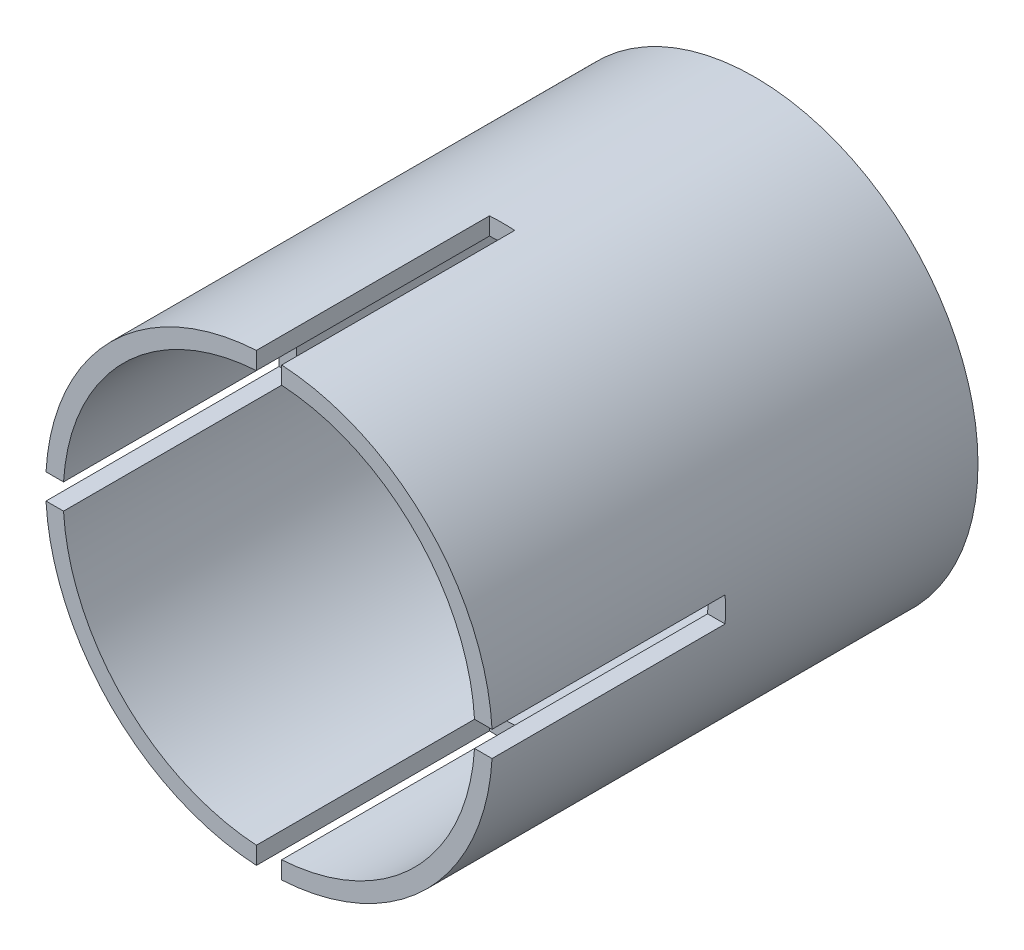
SolidWorks part; units mm, degrees
ref_plane "正面" through (0, 0, 0) normal (0, 0, 1) x (1, 0, 0)
ref_plane "平面" through (0, 0, 0) normal (0, 1, 0) x (1, 0, 0)
ref_plane "右側面" through (0, 0, 0) normal (1, 0, 0) x (0, 0, -1)
sketch "ｽｹｯﾁ1" plane through (0, 0, 0) normal (0, 0, 1) x (1, 0, 0)
  circle A0 centre (0, 0) radius 10.6
  circle A1 centre (0, 0) radius 11.5
  dimension "D1" = 21.2
  dimension "D2" = 23
extrude "ﾎﾞｽ - 押し出し1" add sketch "ｽｹｯﾁ1" along normal blind 25
sketch "ｽｹｯﾁ2" plane through (0, 0, 0) normal (0, 0, 1) x (1, 0, 0)
  circle A0 centre (0, 0) radius 11.5
extrude "ﾎﾞｽ - 押し出し2" add sketch "ｽｹｯﾁ2" along normal blind 1
sketch "ｽｹｯﾁ3" plane through (0, 0, 25) normal (0, 0, 1) x (1, 0, 0)
  line L1 (13, -0.65) -> (10, -0.65)
  line L2 (13, -0.65) -> (13, 0.65)
  line L3 (13, 0.65) -> (10, 0.65)
  line L4 (10, -0.65) -> (10, 0.65)
  line L5 (13, -0.65) -> (10, 0.65) construction
  line L6 (13, 0.65) -> (10, -0.65) construction
  circle A0 centre (0, 0) radius 11.5 construction
  point P0 (11.5, 0)
  dimension "D1" = 1.3
  dimension "D2" = 3
extrude "ｶｯﾄ - 押し出し4" cut sketch "ｽｹｯﾁ3" against normal blind 12
pattern_circular "円形ﾊﾟﾀｰﾝ1" count 4 over 360 about axis through (0, 0, 0) along (0, 0, 1) of "ｶｯﾄ - 押し出し4"
